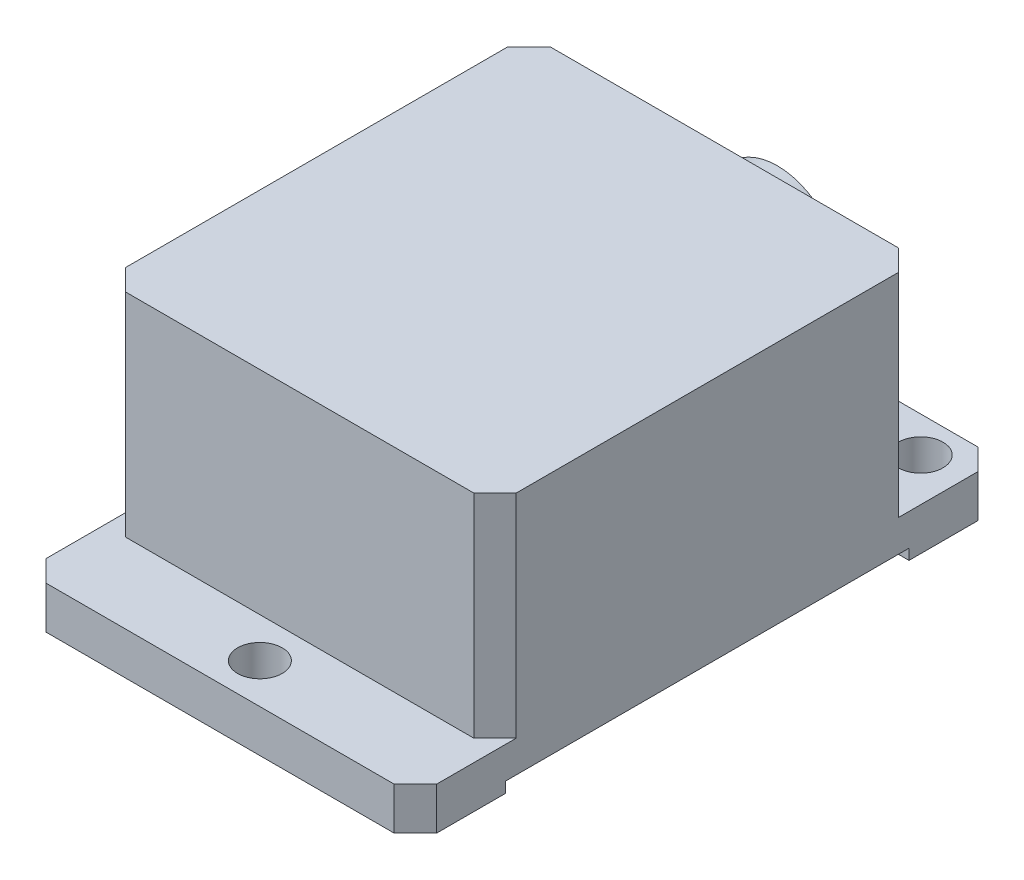
SolidWorks part; units mm, degrees
ref_plane "Front Plane" through (0, 0, 0) normal (0, 0, 1) x (1, 0, 0)
ref_plane "Top Plane" through (0, 0, 0) normal (0, 1, 0) x (1, 0, 0)
ref_plane "Right Plane" through (0, 0, 0) normal (1, 0, 0) x (0, 0, -1)
sketch "Sketch3" plane through (0, 0, 0) normal (0, 1, 0) x (1, 0, 0)
  line L1 (0, 0) -> (36.8, 0)
  line L2 (0, 0) -> (0, 55)
  line L3 (0, 55) -> (36.8, 55)
  line L4 (36.8, 0) -> (36.8, 55)
  dimension "D1" = 55
  dimension "D2" = 36.8
extrude "Boss-Extrude2" add sketch "Sketch3" along normal blind 24
sketch "Sketch4" plane through (36.8, 0, 0) normal (1, 0, 0) x (0, 0, -1)
  line L0 (0, 0) -> (55, 0) construction
  line L1 (8.5, 0) -> (46.5, 0)
  line L2 (8.5, 0) -> (8.5, 1)
  line L3 (8.5, 1) -> (46.5, 1)
  line L4 (46.5, 0) -> (46.5, 1)
  line L5 (27.5, 24) -> (27.5, 0) construction
  line L6 (0, 24) -> (55, 24) construction
  line L7 (55, 24) -> (55, 0) construction
  line L8 (55, 4) -> (47.5, 4)
  line L9 (55, 4) -> (55, 24)
  line L10 (55, 24) -> (47.5, 24)
  line L11 (47.5, 4) -> (47.5, 24)
  line L12 (7.5, 4) -> (7.5, 24)
  line L13 (0, 24) -> (7.5, 24)
  line L14 (0, 4) -> (0, 24)
  line L15 (0, 4) -> (7.5, 4)
  dimension "D1" = 1
  dimension "D2" = 38
  dimension "D3" = 4
  dimension "D4" = 7.5
extrude "Cut-Extrude1" cut sketch "Sketch4" against normal through all
sketch "Sketch5" plane through (0, 4, 0) normal (0, 1, 0) x (1, 0, 0)
  line L0 (18.4, 0) -> (18.4, 7.5) construction
  line L1 (0, 0) -> (36.8, 0) construction
  line L2 (0, 7.5) -> (36.8, 7.5) construction
  line L3 (18.4, 55) -> (18.4, 47.5) construction
  line L4 (0, 55) -> (36.8, 55) construction
  line L5 (0, 47.5) -> (36.8, 47.5) construction
  circle A0 centre (18.4, 3.75) radius 2.1
  circle A1 centre (32.75, 51.65) radius 2.1
  circle A2 centre (4.05, 51.65) radius 2.1
  dimension "D1" = 4.2
  dimension "D2" = 28.7
  dimension "D3" = 47.9
extrude "Cut-Extrude2" cut sketch "Sketch5" against normal through all
chamfer "Chamfer1" distance 2 angle 45 8 edges at (0, 2, -55) (0, 14, -47.5) (36.8, 2, -55) (36.8, 14, -47.5) (36.8, 14, -7.5) (0, 14, -7.5) (0, 2, 0) (36.8, 2, 0)
sketch "Sketch6" plane through (0, 0, -47.5) normal (0, 0, -1) x (-1, 0, 0)
  line L0 (-36.8, 14) -> (0, 14) construction
  line L1 (-36.8, 4) -> (-36.8, 24) construction
  line L2 (0, 24) -> (0, 4) construction
  line L3 (-18.4, 24) -> (-18.4, 4) construction
  line L4 (-2, 24) -> (-34.8, 24) construction
  line L5 (-2, 4) -> (-34.8, 4) construction
  circle A0 centre (-18.4, 14) radius 6
  dimension "D1" = 12
extrude "Boss-Extrude3" add sketch "Sketch6" along normal blind 5
